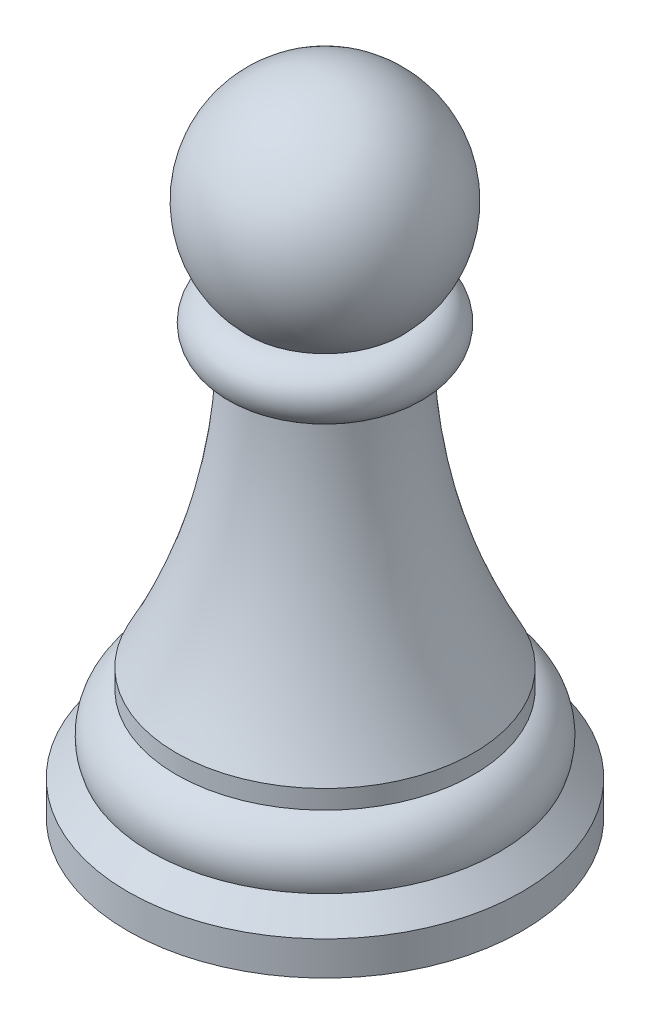
SolidWorks part; units mm, degrees
ref_plane "Front Plane" through (0, 0, 0) normal (0, 0, 1) x (1, 0, 0)
ref_plane "Top Plane" through (0, 0, 0) normal (0, 1, 0) x (1, 0, 0)
ref_plane "Right Plane" through (0, 0, 0) normal (1, 0, 0) x (0, 0, -1)
sketch "Sketch1" plane through (0, 0, 0) normal (0, 0, 1) x (1, 0, 0)
  line L2 (0, 0) -> (0, 20.7188)
  line L4 (0, 0) -> (6.35, 0)
  line L5 (6.35, 0) -> (6.35, 1.0939)
  line L6 (6.35, 1.0939) -> (5.6113, 1.8326)
  line L7 (4.7875, 3.5784) -> (4.7875, 4.184)
  arc A2 (2.4828, 14.6804) -> (2.4828, 12.9143) centre (2.4828, 13.7973) cw
  arc A3 (5.6113, 1.8326) -> (4.7875, 3.5784) centre (4.3265, 2.2936) ccw
  arc A4 (2.4828, 14.6804) -> (0, 20.7188) centre (0, 17.1891) ccw
  spline S0 degree 2 poles (2.4828, 12.9143) (2.5834, 8.2869) (4.7875, 4.184) knots 0 0 0 1 1 1
  point P17 (6.35, 0)
  dimension "D2" = 20.7188
  dimension "D3" = 1.0939
  dimension "D5" = 1.365
  dimension "D6" = 0.883
  dimension "D7" = 9.1155
  dimension "D8" = 3.5297
  dimension "D1" = 6.35
  dimension "D4" = 0.6056
revolve "Revolve4" add sketch "Sketch1" angle 360 about L2
